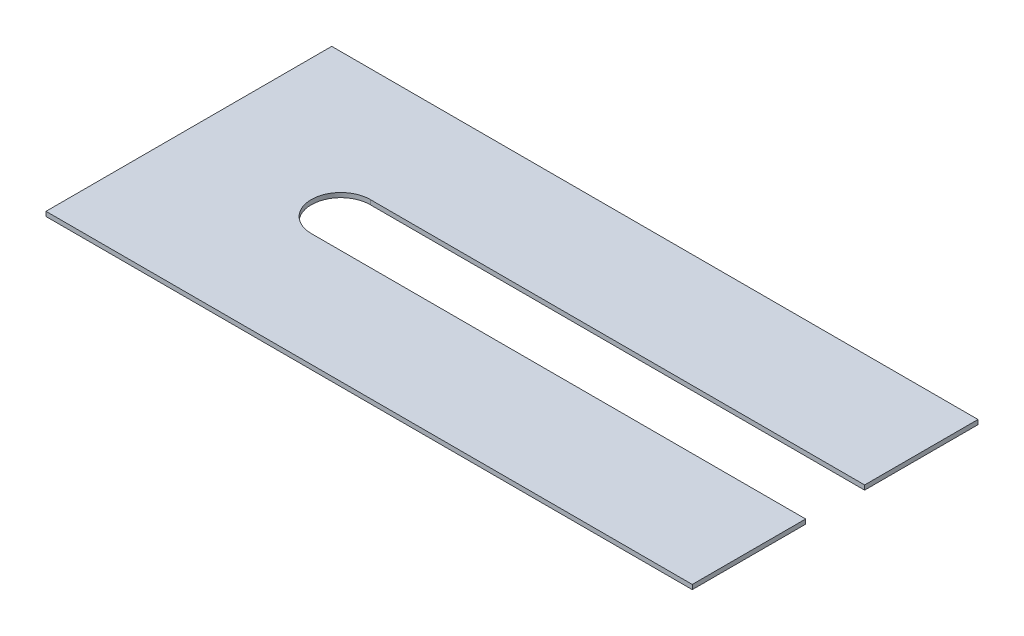
SolidWorks part; units mm, degrees
ref_plane "Front Plane" through (0, 0, 0) normal (0, 0, 1) x (1, 0, 0)
ref_plane "Top Plane" through (0, 0, 0) normal (0, 1, 0) x (1, 0, 0)
ref_plane "Right Plane" through (0, 0, 0) normal (1, 0, 0) x (0, 0, -1)
sketch "Sketch1" plane through (0, 0, 0) normal (0, 1, 0) x (1, 0, 0)
  line L0 (71.25, 15.75) -> (16.75, 15.75) construction
  line L1 (0, 0) -> (71.25, 0)
  line L2 (0, 0) -> (0, 31.5)
  line L3 (0, 31.5) -> (71.25, 31.5)
  line L4 (71.25, 0) -> (71.25, 31.5)
  line L5 (0, 0) -> (71.25, 31.5) construction
  line L6 (0, 31.5) -> (71.25, 0) construction
  line L7 (71.25, 12.5) -> (16.75, 12.5)
  line L8 (71.25, 19) -> (16.75, 19)
  line L9 (71.25, 19) -> (71.25, 12.5)
  arc A0 (71.25, 12.5) -> (71.25, 19) centre (71.25, 15.75) ccw
  arc A1 (16.75, 19) -> (16.75, 12.5) centre (16.75, 15.75) ccw
  point P4 (35.625, 15.75)
  point P8 (44, 15.75)
  point P13 (13.5, 15.75)
  dimension "D1" = 31.5
  dimension "D2" = 71.25
  dimension "D3" = 6.5
  dimension "D4" = 13.5
extrude "Boss-Extrude1" add sketch "Sketch1" along normal blind 0.5 contours A1 L8 L4 L3 L2 L1 L7
